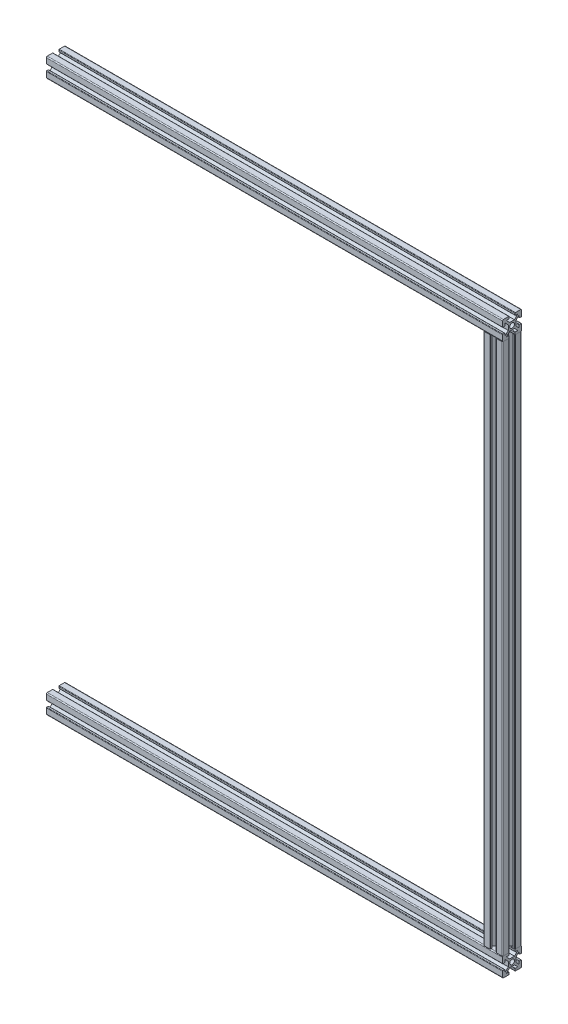
SolidWorks part; units mm, degrees
ref_plane "Front Plane" through (0, 0, 0) normal (0, 0, 1) x (1, 0, 0)
ref_plane "Top Plane" through (0, 0, 0) normal (0, 1, 0) x (1, 0, 0)
ref_plane "Right Plane" through (0, 0, 0) normal (1, 0, 0) x (0, 0, -1)
sketch "Sketch1" plane through (0, 0, 0) normal (0, 0, 1) x (1, 0, 0)
  line L0 (-195.4211, 179.3421) -> (274.5789, 179.3421)
  line L1 (274.5789, 179.3421) -> (274.5789, -400.6579)
  line L2 (274.5789, -400.6579) -> (-195.4211, -400.6579)
  dimension "D1" = 470
  dimension "D2" = 470
  dimension "D3" = 580
other "Aluminium prof ALUMINIUM PROF(1)"
ref_plane "Plane1" through (-195.4211, 179.3421, 0) normal (1, 0, 0) x (0, 1, 0)
sketch "Sketch11" plane through (-195.4211, 179.3421, 0) normal (1, 0, 0) x (0, 1, 0)
  line L0 (0, 0) -> (0, 19.0058) construction
  line L9 (0, 0) -> (23.0409, 0) construction
  line L10 (23.0409, 0) -> (23.0409, -0.0585) construction
  line L11 (23.0409, -0.0585) -> (23.0409, 0) construction
  line L13 (-2.5, 4) -> (2.5, 4)
  line L14 (2.5, 4) -> (6.0355, 7.5355)
  line L15 (6.0355, 7.5355) -> (3.5355, 7.5355)
  line L16 (3.0355, 8.0355) -> (3.0355, 9.5355)
  line L17 (3.5355, 10.0355) -> (9.0355, 10.0355)
  line L18 (10.0355, 9.0355) -> (10.0355, 3.5355)
  line L19 (9.5355, 3.0355) -> (8.0355, 3.0355)
  line L20 (7.5355, 3.5355) -> (7.5355, 6.0355)
  line L21 (7.5355, 6.0355) -> (4, 2.5)
  line L22 (4, 2.5) -> (4, -2.5)
  line L23 (-10.0355, 9.0355) -> (-10.0355, 3.5355)
  line L24 (-4, 2.5) -> (-4, -2.5)
  line L25 (-7.5355, 6.0355) -> (-4, 2.5)
  line L26 (-7.5355, 3.5355) -> (-7.5355, 6.0355)
  line L27 (-9.5355, 3.0355) -> (-8.0355, 3.0355)
  line L28 (-3.5355, 10.0355) -> (-9.0355, 10.0355)
  line L29 (-3.0355, 8.0355) -> (-3.0355, 9.5355)
  line L30 (-6.0355, 7.5355) -> (-3.5355, 7.5355)
  line L31 (-2.5, 4) -> (-6.0355, 7.5355)
  line L32 (3.5355, -10.0355) -> (9.0355, -10.0355)
  line L33 (-2.5, -4) -> (-6.0355, -7.5355)
  line L34 (-6.0355, -7.5355) -> (-3.5355, -7.5355)
  line L35 (-3.0355, -8.0355) -> (-3.0355, -9.5355)
  line L36 (-3.5355, -10.0355) -> (-9.0355, -10.0355)
  line L37 (-9.5355, -3.0355) -> (-8.0355, -3.0355)
  line L38 (-7.5355, -3.5355) -> (-7.5355, -6.0355)
  line L39 (-7.5355, -6.0355) -> (-4, -2.5)
  line L40 (-10.0355, -9.0355) -> (-10.0355, -3.5355)
  line L41 (7.5355, -6.0355) -> (4, -2.5)
  line L42 (7.5355, -3.5355) -> (7.5355, -6.0355)
  line L43 (9.5355, -3.0355) -> (8.0355, -3.0355)
  line L44 (10.0355, -9.0355) -> (10.0355, -3.5355)
  line L45 (3.0355, -8.0355) -> (3.0355, -9.5355)
  line L46 (6.0355, -7.5355) -> (3.5355, -7.5355)
  line L47 (2.5, -4) -> (6.0355, -7.5355)
  line L48 (-2.5, -4) -> (2.5, -4)
  circle A0 centre (0, 0) radius 2.5
  arc A1 (-10.0355, 9.0355) -> (-9.0355, 10.0355) centre (-9.0355, 9.0355) cw
  arc A2 (-9.0355, -10.0355) -> (-10.0355, -9.0355) centre (-9.0355, -9.0355) cw
  arc A3 (9.0355, -10.0355) -> (10.0355, -9.0355) centre (9.0355, -9.0355) ccw
  arc A4 (9.0355, 10.0355) -> (10.0355, 9.0355) centre (9.0355, 9.0355) cw
  arc A5 (-9.5355, -3.0355) -> (-10.0355, -3.5355) centre (-9.5355, -3.5355) ccw
  arc A6 (-8.0355, -3.0355) -> (-7.5355, -3.5355) centre (-8.0355, -3.5355) cw
  arc A7 (-3.5355, -7.5355) -> (-3.0355, -8.0355) centre (-3.5355, -8.0355) cw
  arc A8 (-3.0355, -9.5355) -> (-3.5355, -10.0355) centre (-3.5355, -9.5355) cw
  arc A9 (3.5355, -10.0355) -> (3.0355, -9.5355) centre (3.5355, -9.5355) cw
  arc A10 (3.0355, -8.0355) -> (3.5355, -7.5355) centre (3.5355, -8.0355) cw
  arc A11 (9.5355, -3.0355) -> (10.0355, -3.5355) centre (9.5355, -3.5355) cw
  arc A12 (7.5355, -3.5355) -> (8.0355, -3.0355) centre (8.0355, -3.5355) cw
  arc A13 (10.0355, 3.5355) -> (9.5355, 3.0355) centre (9.5355, 3.5355) cw
  arc A14 (8.0355, 3.0355) -> (7.5355, 3.5355) centre (8.0355, 3.5355) cw
  arc A15 (3.5355, 7.5355) -> (3.0355, 8.0355) centre (3.5355, 8.0355) cw
  arc A16 (3.0355, 9.5355) -> (3.5355, 10.0355) centre (3.5355, 9.5355) cw
  arc A17 (-3.5355, 10.0355) -> (-3.0355, 9.5355) centre (-3.5355, 9.5355) cw
  arc A18 (-3.0355, 8.0355) -> (-3.5355, 7.5355) centre (-3.5355, 8.0355) cw
  arc A19 (-7.5355, 3.5355) -> (-8.0355, 3.0355) centre (-8.0355, 3.5355) cw
  arc A20 (-10.0355, 3.5355) -> (-9.5355, 3.0355) centre (-9.5355, 3.5355) ccw
  point P26 (0, 4)
  point P29 (-4, 0)
  point P30 (4, 0)
  point P44 (0, -4)
  point P48 (-10.0355, 10.0355)
  point P51 (-10.0355, -10.0355)
  point P54 (10.0355, -10.0355)
  point P57 (10.0355, 10.0355)
  point P60 (-10.0355, -3.0355)
  point P63 (-7.5355, -3.0355)
  point P66 (-3.0355, -7.5355)
  point P69 (-3.0355, -10.0355)
  point P72 (3.0355, -10.0355)
  point P75 (3.0355, -7.5355)
  point P78 (10.0355, -3.0355)
  point P81 (7.5355, -3.0355)
  point P84 (10.0355, 3.0355)
  point P87 (7.5355, 3.0355)
  point P90 (3.0355, 7.5355)
  point P93 (3.0355, 10.0355)
  point P96 (-3.0355, 10.0355)
  point P99 (-3.0355, 7.5355)
  point P102 (-7.5355, 3.0355)
  point P105 (-10.0355, 3.0355)
  point P106 (0, 0)
  dimension "D5" = 4
  dimension "D12" = 1
  dimension "D13" = 0.5
  dimension "D1" = 135
  dimension "D2" = 2.5
  dimension "D3" = 4
  dimension "D4" = 2.5
  dimension "D6" = 7
  dimension "D7" = 7
  dimension "D8" = 3
  dimension "D9" = 3
  dimension "D10" = 5
  dimension "D11" = 23.0409
other "Trim/Extend1"
other "Trim/Extend2"
